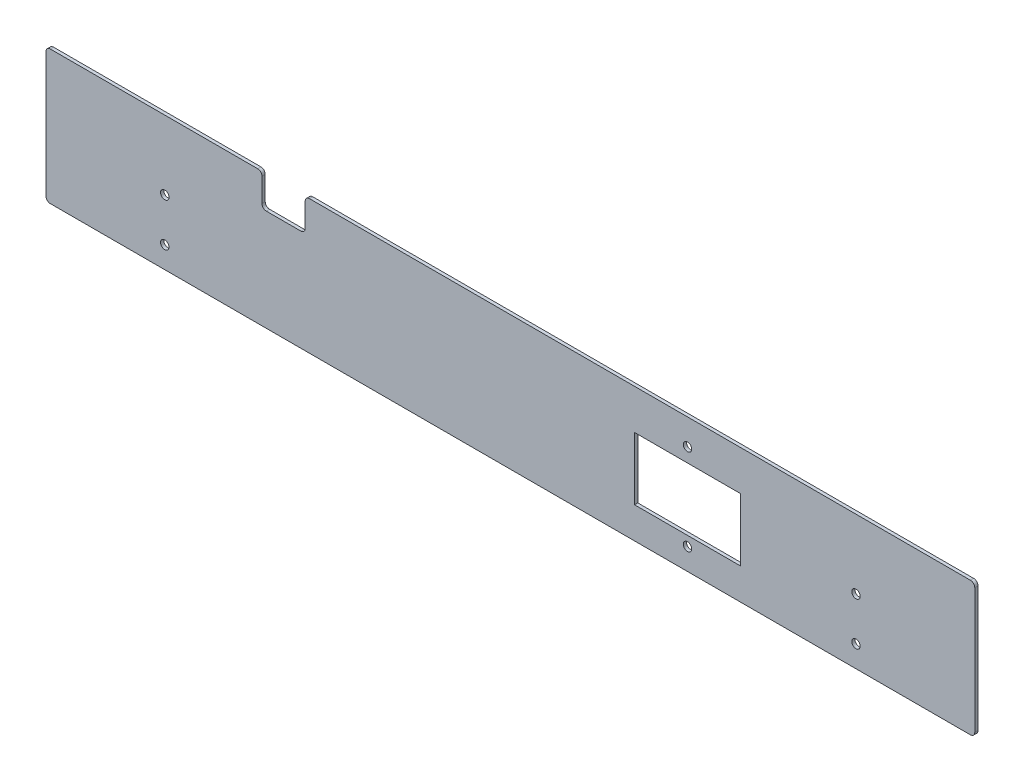
SolidWorks part; units mm, degrees
ref_plane "Front Plane" through (0, 0, 0) normal (0, 0, 1) x (1, 0, 0)
ref_plane "Top Plane" through (0, 0, 0) normal (0, 1, 0) x (1, 0, 0)
ref_plane "Right Plane" through (0, 0, 0) normal (1, 0, 0) x (0, 0, -1)
sketch "Sketch1" plane through (0, 0, 0) normal (0, 0, 1) x (1, 0, 0)
  line L0 (-231.9248, 29.7035) -> (78.0752, 29.7035)
  line L1 (-351.9248, 29.7035) -> (-251.9248, 29.7035)
  line L2 (-351.9248, 29.7035) -> (-351.9248, -32.2965)
  line L3 (-351.9248, -32.2965) -> (78.0752, -32.2965)
  line L4 (78.0752, 29.7035) -> (78.0752, -32.2965)
  line L5 (-79.4248, 11.2035) -> (-30.4248, 11.2035)
  line L6 (-79.4248, 11.2035) -> (-79.4248, -17.7965)
  line L7 (-79.4248, -17.7965) -> (-30.4248, -17.7965)
  line L8 (-30.4248, 11.2035) -> (-30.4248, -17.7965)
  line L10 (-231.9248, 29.7035) -> (-231.9248, 14.7035)
  line L11 (-231.9248, 14.7035) -> (-251.9248, 14.7035)
  line L12 (-251.9248, 29.7035) -> (-251.9248, 14.7035)
  circle A0 centre (-54.9248, 17.7035) radius 1.95
  circle A1 centre (-54.9248, -22.2965) radius 1.95
  point P12 (-54.9248, 11.2035)
  dimension "D3" = 133
  dimension "D4" = 40
  dimension "D1" = 430
  dimension "D2" = 62
  dimension "D5" = 10
  dimension "D6" = 49
  dimension "D7" = 29
  dimension "D8" = 6.5
  dimension "D9" = 20
  dimension "D10" = 100
  dimension "D11" = 15
extrude "Boss-Extrude1" add sketch "Sketch1" along normal blind 1.5
fillet "Fillet1" radius 2 8 edges at (78.0752, -32.2965, 0.75) (-351.9248, -32.2965, 0.75) (-351.9248, 29.7035, 0.75) (-231.9248, 14.7035, 0.75) (-251.9248, 14.7035, 0.75) (-251.9248, 29.7035, 0.75) (-231.9248, 29.7035, 0.75) (78.0752, 29.7035, 0.75)
sketch "Sketch3" plane through (0, 0, 0) normal (0, 0, -1) x (-1, 0, 0)
  line L0 (349.9248, -32.2965) -> (-76.0752, -32.2965) construction
  line L1 (-78.0752, -30.2965) -> (-78.0752, 27.7035) construction
  line L2 (351.9248, 27.7035) -> (351.9248, -30.2965) construction
  circle A0 centre (-23.0752, -22.2965) radius 1.95
  circle A1 centre (-23.0752, -2.2965) radius 1.95
  circle A2 centre (296.9248, -22.2965) radius 1.95
  circle A3 centre (296.9248, -2.2965) radius 1.95
  dimension "D1" = 10
  dimension "D3" = 20
  dimension "D4" = 55
  dimension "D2" = 55
  dimension "D5" = 20
  dimension "D6" = 10
extrude "Cut-Extrude1" cut sketch "Sketch3" against normal blind 10
